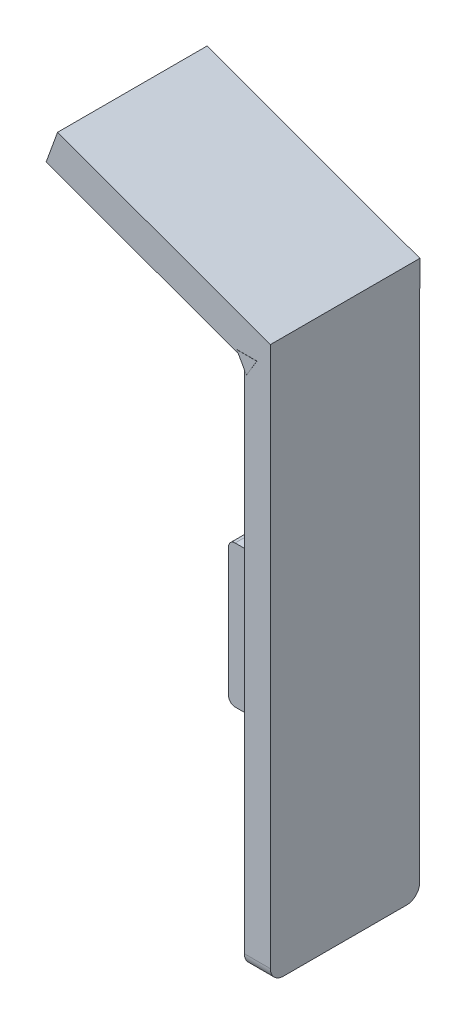
SolidWorks part; units mm, degrees
ref_plane "Plan de face" through (0, 0, 0) normal (0, 0, 1) x (1, 0, 0)
ref_plane "Plan de dessus" through (0, 0, 0) normal (0, 1, 0) x (1, 0, 0)
ref_plane "Plan de droite" through (0, 0, 0) normal (1, 0, 0) x (0, 0, -1)
sketch "Esquisse1" plane through (0, 0, 0) normal (0, 0, 1) x (1, 0, 0)
  line L0 (0, 26.549) -> (0, -58.451)
  line L1 (0, -58.451) -> (-4, -58.451)
  line L2 (-4, -58.451) -> (-4, 26.549)
  line L8 (-4, 26.549) -> (0, 26.549)
extrude "Boss.-Extru.1" add sketch "Esquisse1" along normal blind 22.93
sketch "Esquisse2" plane through (0, 0, 22.93) normal (0, 0, 1) x (1, 0, 0)
  line L4 (-32.6819, 38.4443) -> (0, 26.549)
  line L5 (-4, 26.549) -> (-4, -58.451) construction
  line L6 (0, 26.549) -> (0, 22.549)
  line L7 (0, -58.451) -> (0, 26.549) construction
  line L8 (0, 22.549) -> (-4, 22.549)
  line L9 (-4, 22.549) -> (-34.4354, 33.6266)
  line L10 (-34.4354, 33.6266) -> (-32.6819, 38.4443)
extrude "Boss.-Extru.5" add sketch "Esquisse2" against normal blind 22.95
sketch "Esquisse5" plane through (0, 0, 22.93) normal (0, 0, 1) x (1, 0, 0)
  line L1 (0, -58.451) -> (0, 26.549) construction
  line L2 (0, -21.471) -> (-25.35, -21.471)
  line L5 (-25.35, -21.471) -> (-25.35, -32.571)
  line L6 (-25.35, -32.571) -> (0, -32.571)
  line L7 (0, -32.571) -> (0, -21.471)
sketch "Esquisse7" plane through (0, 0, 0) normal (1, 0, 0) x (0, 0, -1)
  line L0 (0, -43.2913) -> (0, -21.471)
  line L1 (0, 22.549) -> (0, -58.451) construction
  line L2 (-22.93, -32.571) -> (-22.93, -21.471) construction
  line L4 (0, -21.471) -> (0, -43.2913) construction
  line L6 (0, -43.2913) -> (-4, -43.2913)
  line L7 (-4, -43.2913) -> (-4, -21.471)
  line L8 (-4, -21.471) -> (0, -21.471)
fillet "Congé1" radius 2 2 edges at (-2, -58.451, 0) (-2, -58.451, 22.93)
extrude "Boss.-Extru.10" add sketch "Esquisse7" against normal blind 25.35
fillet "Congé14" radius 1 2 edges at (-25.35, -43.2913, 2) (-25.35, -21.471, 2)
fillet "Congé15" radius 1 5 edges at (-25.0571, -42.9984, 0) (-25.35, -32.3812, 0) (-25.0571, -21.7639, 0) (-14.175, -43.2913, 0) (-14.175, -21.471, 0)
sketch "Esquisse10" plane through (-4, 0, 0) normal (-1, 0, 0) x (0, 0, 1)
  line L0 (7.7514, 10.4645) -> (12.7514, 10.4645)
  line L1 (12.7514, 10.4645) -> (12.7514, 15.4645)
  line L2 (12.7514, 15.4645) -> (10.7514, 15.4645)
  line L3 (10.7514, 15.4645) -> (10.7514, 12.4645)
  line L4 (10.7514, 12.4645) -> (7.7514, 12.4645)
  line L5 (7.7514, 12.4645) -> (7.7514, 10.4645)
extrude "Boss.-Extru.11" add sketch "Esquisse10" along normal blind 1
sketch "Esquisse12" plane through (0, 0, 0) normal (1, 0, 0) x (0, 0, -1)
  line L0 (0, -34.7689) -> (-4, -34.7689) construction
  line L1 (0, -56.451) -> (0, 22.549) construction
sketch "Esquisse13" plane through (0, 0, 0) normal (0, 0, 1) x (1, 0, 0)
  line L3 (-5.152, 23.3206) -> (-3.6562, 20.6811)
  line L4 (-3.6562, 20.6811) -> (-2.0751, 23.3206)
  line L5 (-2.0751, 23.3206) -> (-5.152, 23.3206)
extrude "Boss.-Extru.12" add sketch "Esquisse13" along normal blind 22.95
